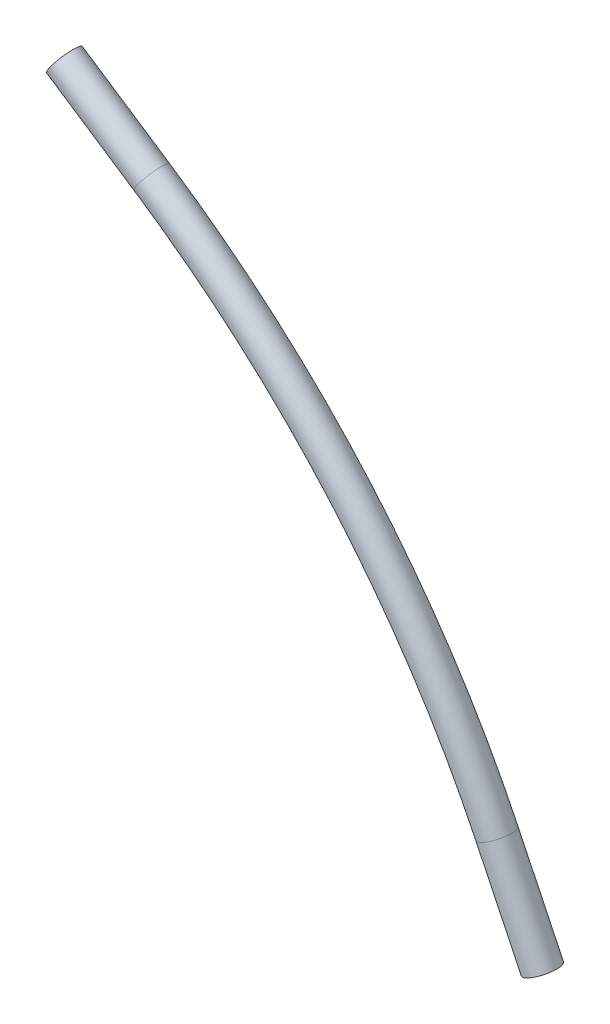
SolidWorks part; units mm, degrees
material "Aço cromo inoxidável"
ref_plane "Plano frontal" through (0, 0, 0) normal (0, 0, 1) x (1, 0, 0)
ref_plane "Plano superior" through (0, 0, 0) normal (0, 1, 0) x (1, 0, 0)
ref_plane "Plano direito" through (0, 0, 0) normal (1, 0, 0) x (0, 0, -1)
sketch "Esboço1" plane through (0, 0, 0) normal (0, 0, 1) x (1, 0, 0)
  line L0 (-28.7425, 234.7519) -> (-45.4104, 245.8055)
  line L1 (-30.7155, 231.7767) -> (-26.7694, 237.7272) construction
  line L2 (36.9563, 159.3618) -> (45.6269, 141.339)
  line L4 (40.62, 158.6338) -> (35.248, 155.9614) construction
  line L6 (-47.0684, 243.3054) -> (-43.7523, 248.3057) construction
  arc A2 (-28.7425, 234.7519) -> (36.9563, 159.3618) centre (-132.9454, 77.6227) cw
  point P2 (37.934, 157.2976)
  dimension "D1" = 100
  dimension "D2" = 20
sweep "Varredura1" add path "Esboço1" circular profile diameter 6 parameters "D3"=6
chamfer "Chanfro1" [suppressed] distance 0.5 angle 45
